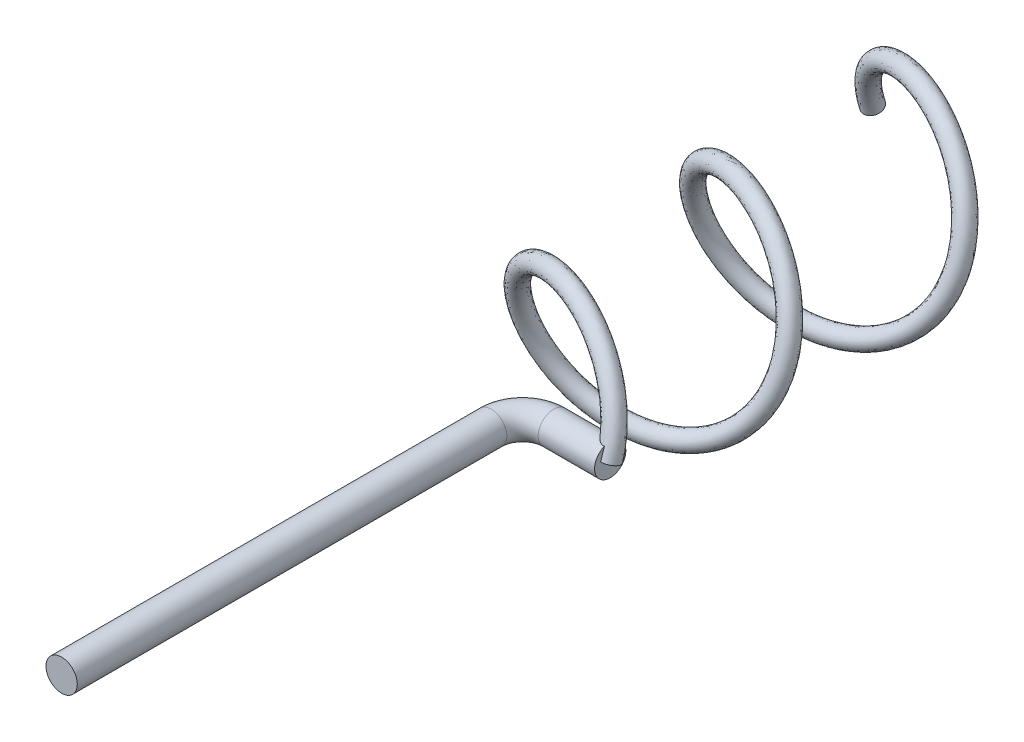
SolidWorks part; units mm, degrees
ref_plane "Front Plane" through (0, 0, 0) normal (0, 0, 1) x (1, 0, 0)
ref_plane "Top Plane" through (0, 0, 0) normal (0, 1, 0) x (1, 0, 0)
ref_plane "Right Plane" through (0, 0, 0) normal (1, 0, 0) x (0, 0, -1)
sketch "Sketch3" plane through (0, 0, 0) normal (0, 0, 1) x (1, 0, 0)
  circle A0 centre (0, 0) radius 14
curve "Helix/Spiral1" pitch 28 height 70 turns 2.5
sketch "Sketch4" plane through (0, 0, 0) normal (0, 1, 0) x (1, 0, 0)
  line L0 (0, -74.9036) -> (0, -143.4844)
  line L1 (5, -69.9036) -> (14, -69.9036)
  arc A0 (0, -74.9036) -> (5, -69.9036) centre (5, -74.9036) cw
  dimension "D1" = 5
sweep "Sweep2" add path "Sketch4" circular profile diameter 5 parameters "D3"=5
sweep "Sweep3" add path "Helix/Spiral1" circular profile diameter 3 parameters "D3"=3
